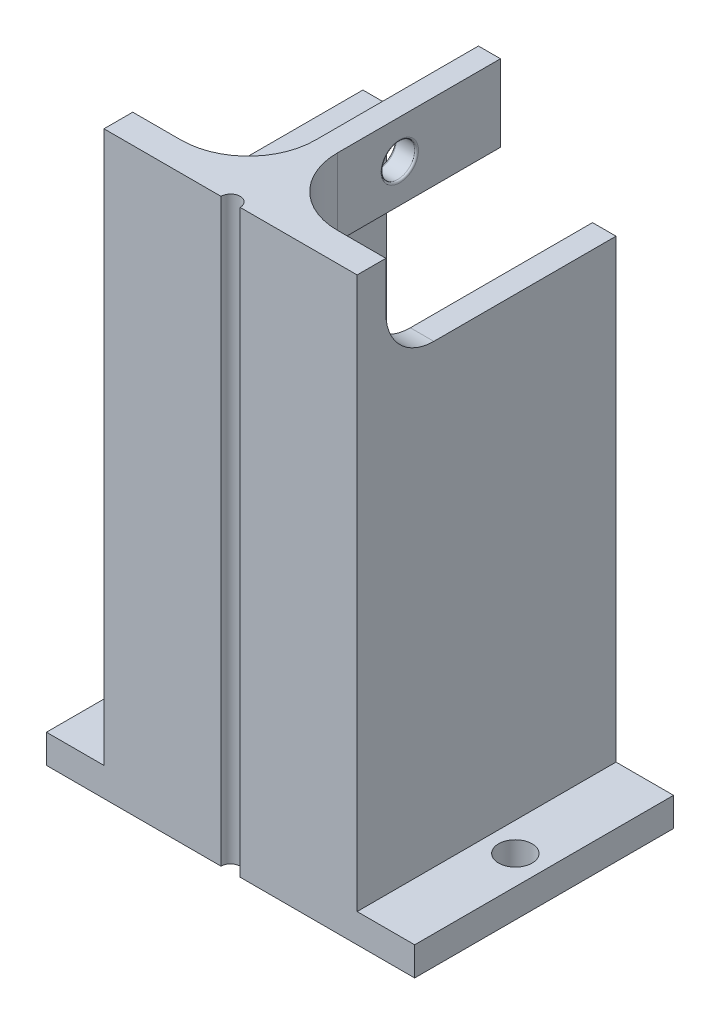
SolidWorks part; units mm, degrees
ref_plane "正面" through (0, 0, 0) normal (0, 0, 1) x (1, 0, 0)
ref_plane "平面" through (0, 0, 0) normal (0, 1, 0) x (1, 0, 0)
ref_plane "右側面" through (0, 0, 0) normal (1, 0, 0) x (0, 0, -1)
sketch "ｽｹｯﾁ1" plane through (0, 0, 0) normal (0, 0, 1) x (1, 0, 0)
  line L1 (13.2, 30.25) -> (-13.2, 30.25)
  line L2 (13.2, 30.25) -> (13.2, -30.25)
  line L3 (13.2, -30.25) -> (-13.2, -30.25)
  line L4 (-13.2, 30.25) -> (-13.2, -30.25)
  line L5 (13.2, 30.25) -> (-13.2, -30.25) construction
  line L6 (13.2, -30.25) -> (-13.2, 30.25) construction
  point P0 (0, 0)
  dimension "D1" = 26.4
  dimension "D2" = 60.5
extrude "ﾎﾞｽ - 押し出し1" add sketch "ｽｹｯﾁ1" along normal blind 27
sketch "ｽｹｯﾁ3" plane through (0, 0, 0) normal (0, 0, -1) x (-1, 0, 0)
  line L0 (13.2, -30.25) -> (-13.2, -30.25) construction
  line L1 (10.75, 30.25) -> (-10.75, 30.25)
  line L2 (10.75, 30.25) -> (10.75, -30.25)
  line L3 (10.75, -30.25) -> (-10.75, -30.25)
  line L4 (-10.75, 30.25) -> (-10.75, -30.25)
  line L5 (10.75, 30.25) -> (-10.75, -30.25) construction
  line L6 (10.75, -30.25) -> (-10.75, 30.25) construction
  point P0 (0, 0)
  dimension "D1" = 21.5
extrude "ｶｯﾄ - 押し出し1" cut sketch "ｽｹｯﾁ3" against normal blind 24
sketch "ｽｹｯﾁ4" plane through (-13.2, 0, 0) normal (-1, 0, 0) x (0, 0, 1)
  line L1 (0, 30.25) -> (24, 30.25)
  line L2 (0, 30.25) -> (0, 20.25)
  line L3 (0, 20.25) -> (24, 20.25)
  line L4 (24, 30.25) -> (24, 20.25)
  dimension "D1" = 10
  dimension "D2" = 24
extrude "ｶｯﾄ - 押し出し2" cut sketch "ｽｹｯﾁ4" against normal through all
sketch "ｽｹｯﾁ7" plane through (0, 0, 24) normal (0, 0, -1) x (-1, 0, 0)
  line L0 (13.2, 30.25) -> (-13.2, 30.25) construction
  line L1 (1.15, 30.25) -> (-1.15, 30.25)
  line L2 (1.15, 30.25) -> (1.15, 22.25)
  line L3 (1.15, 22.25) -> (-1.15, 22.25)
  line L4 (-1.15, 30.25) -> (-1.15, 22.25)
  line L5 (1.15, 30.25) -> (-1.15, 22.25) construction
  line L6 (1.15, 22.25) -> (-1.15, 30.25) construction
  line L7 (-10.75, -30.25) -> (10.75, -30.25) construction
  point P0 (0, 26.25)
  point P7 (0, -30.25)
  dimension "D1" = 2.3
  dimension "D2" = 0
  dimension "D3" = 8
  dimension "D4" = 0
extrude "ﾎﾞｽ - 押し出し3" add sketch "ｽｹｯﾁ7" along normal blind 24
sketch "ｽｹｯﾁ9" plane through (1.15, 0, 0) normal (1, 0, 0) x (0, 0, -1)
  line L0 (-24, 30.25) -> (-24, 22.25) construction
  line L1 (0, 30.25) -> (-24, 30.25) construction
  circle A0 centre (-10.5, 26.25) radius 1.75
  dimension "D3" = 3.5
  dimension "D1" = 13.5
  dimension "D2" = 4
extrude "ｶｯﾄ - 押し出し4" cut sketch "ｽｹｯﾁ9" against normal up to next
fillet "ﾌｨﾚｯﾄ1" radius 7 1 edges at (1.15, 26.25, 24)
fillet "ﾌｨﾚｯﾄ2" radius 7 1 edges at (-1.15, 26.25, 24)
fillet "ﾌｨﾚｯﾄ3" radius 4 1 edges at (0, 22.25, 24)
fillet "ﾌｨﾚｯﾄ4" radius 0.2 2 edges at (-1.15, 28, 10.5) (1.15, 28, 10.5)
fillet "ﾌｨﾚｯﾄ7" radius 5 2 edges at (11.975, 20.25, 24) (-11.975, 20.25, 24)
sketch "ｽｹｯﾁ10" plane through (0, -30.25, 0) normal (0, -1, 0) x (-1, 0, 0)
  line L0 (12.7, -27) -> (-12.7, -27) construction
  circle A0 centre (0, -27) radius 1
  dimension "D1" = 2
extrude "ｶｯﾄ - 押し出し5" cut sketch "ｽｹｯﾁ10" against normal through all
sketch "ｽｹｯﾁ11" plane through (0, -30.25, 0) normal (0, -1, 0) x (-1, 0, 0)
  line L0 (0, -24) -> (0, 6.6117)
  line L1 (-13.2, -27) -> (-19.2, -27)
  line L2 (-13.2, -27) -> (-13.2, 0)
  line L3 (-13.2, 0) -> (-19.2, 0)
  line L4 (-19.2, -27) -> (-19.2, 0)
  line L5 (-10.75, -24) -> (10.75, -24) construction
  line L6 (13.2, -27) -> (13.2, 0)
  line L7 (13.2, -27) -> (19.2, -27)
  line L8 (13.2, 0) -> (19.2, 0)
  line L9 (19.2, -27) -> (19.2, 0)
  circle A0 centre (-16.2, -13.5) radius 1.75
  circle A1 centre (16.2, -13.5) radius 1.75
  line M9 (13.2, -27) -> (13.2, 0)
  line M15 (-13.2, 0) -> (-13.2, -27)
  dimension "D2" = 3.5
  dimension "D1" = 6
  dimension "D3" = 3
extrude "ﾎﾞｽ - 押し出し4" add sketch "ｽｹｯﾁ11" against normal blind 3 contours L4 L1 L3 A0 M15 | L7 L9 L8 A1 M9
